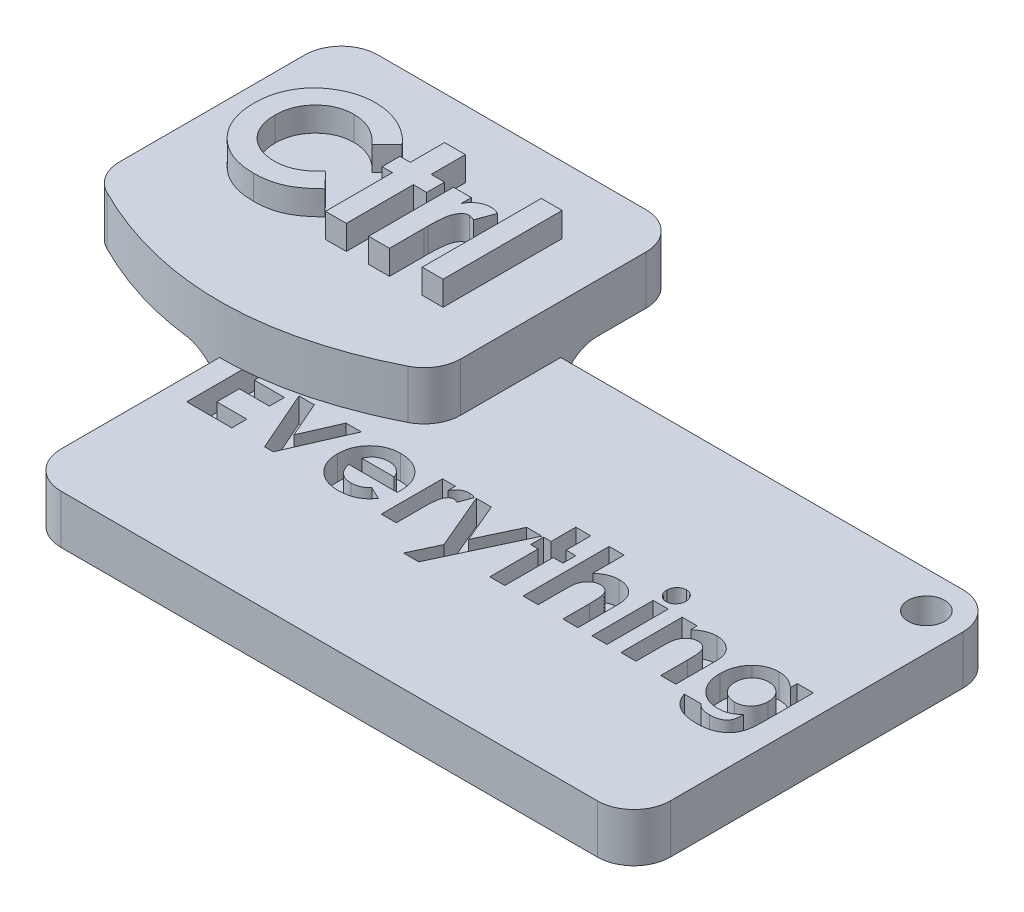
SolidWorks part; units mm, degrees
ref_plane "Front Plane" through (0, 0, 0) normal (0, 0, 1) x (1, 0, 0)
ref_plane "Top Plane" through (0, 0, 0) normal (0, 1, 0) x (1, 0, 0)
ref_plane "Right Plane" through (0, 0, 0) normal (1, 0, 0) x (0, 0, -1)
sketch "草图1" plane through (0, 0, 0) normal (0, 1, 0) x (1, 0, 0)
  line L2 (-14, -10) -> (-14, 10)
  line L3 (-14, 10) -> (14, 10)
  line L4 (14, -10) -> (14, 10)
  line L5 (-14, -10) -> (14, 10) construction
  line L6 (-14, 10) -> (14, -10) construction
  spline S0 degree 2 poles (-14, -10) (0, -18) (14, -10) knots 0 0 0 1 1 1
  point P0 (0, 0)
  dimension "D1" = 28
  dimension "D2" = 20
  dimension "D3" = 20
  dimension "D4" = 4
extrude "凸台-拉伸1" add sketch "草图1" along normal blind 4
sketch "草图2" plane through (0, 4, 0) normal (0, 1, 0) x (1, 0, 0)
  text T0 "<b>Ctrl</b>" font "Century Gothic" height in points 36
extrude "凸台-拉伸2" add sketch "草图2" along normal blind 2
fillet "圆角2" radius 3 4 edges at (14, 2, -10) (14, 2, 10) (-14, 2, 10) (-14, 2, -10)
sketch "草图3" plane through (0, 0, 0) normal (0, -1, 0) x (1, 0, 0)
  line L1 (0, 0) -> (50, 0)
  line L2 (0, 0) -> (0, 30)
  line L3 (0, 30) -> (50, 30)
  line L4 (50, 0) -> (50, 30)
  dimension "D1" = 30
  dimension "D2" = 50
extrude "凸台-拉伸3" add sketch "草图3" along normal blind 4
fillet "圆角3" radius 3 5 edges at (0, 0, 7) (7, 0, 0) (0, -2, 30) (50, -2, 30) (50, -2, 0)
sketch "草图4" plane through (0, 0, 0) normal (0, 1, 0) x (1, 0, 0)
  text T0 "<b>Everything</b>" font "Century Gothic" height in points 26
extrude "切除-拉伸1" cut sketch "草图4" against normal blind 2
sketch "草图5" plane through (0, 0, 0) normal (0, 1, 0) x (1, 0, 0)
  circle A0 centre (47, -3) radius 1.5
  dimension "D1" = 3
extrude "切除-拉伸2" cut sketch "草图5" against normal through all
